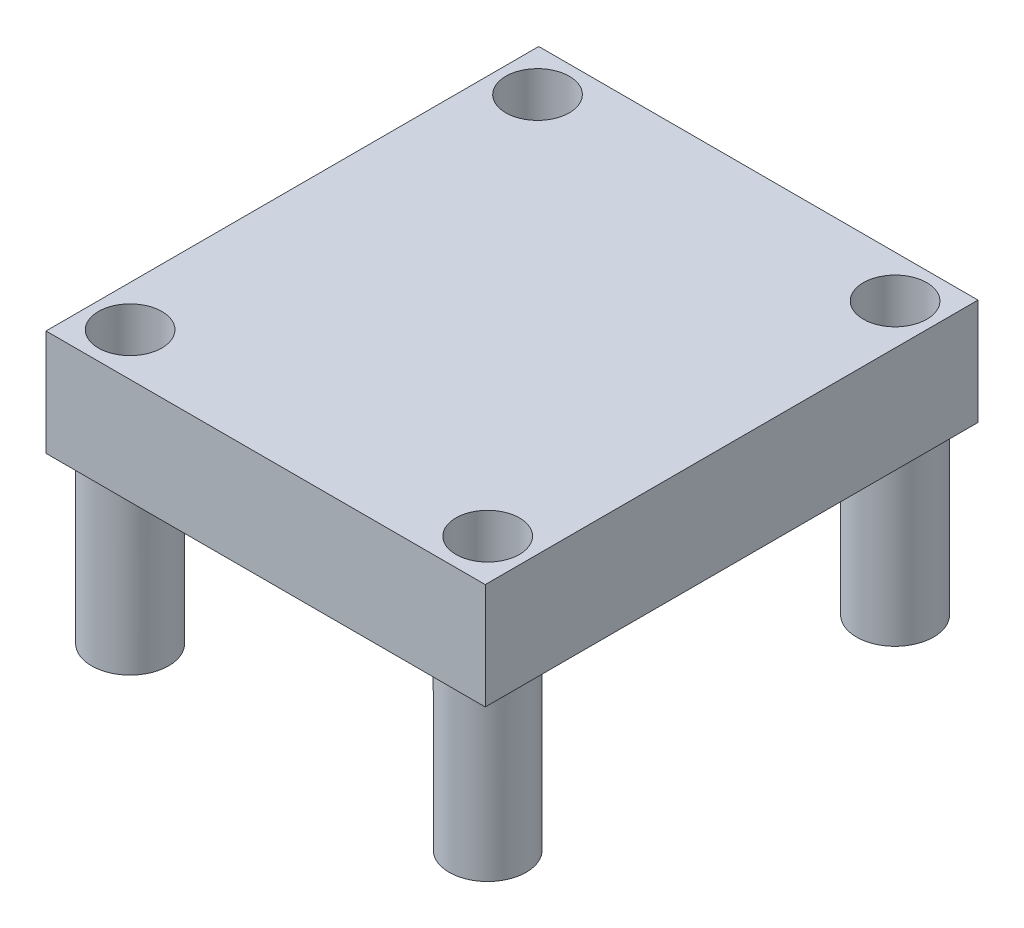
SolidWorks part; units mm, degrees
ref_plane "Front Plane" through (0, 0, 0) normal (0, 0, 1) x (1, 0, 0)
ref_plane "Top Plane" through (0, 0, 0) normal (0, 1, 0) x (1, 0, 0)
ref_plane "Right Plane" through (0, 0, 0) normal (1, 0, 0) x (0, 0, -1)
sketch "Sketch1" plane through (0, 0, 0) normal (0, 1, 0) x (1, 0, 0)
  line L0 (-34.0407, 1.6731) -> (-34.0407, -23.8285)
  line L1 (-34.0407, -23.8285) -> (-11.3077, -23.8285)
  line L2 (-11.3077, -23.8285) -> (-11.3077, 1.6731)
  line L3 (-11.3077, 1.6731) -> (-34.0407, 1.6731)
  dimension "D1" = 25.5016
  dimension "D2" = 22.733
extrude "Boss-Extrude1" add sketch "Sketch1" along normal blind 5.4864
sketch "Sketch2" plane through (0, 0, 0) normal (0, -1, 0) x (1, 0, 0)
  circle A0 centre (-31.9185, 21.5968) radius 1.9939
  circle A1 centre (-13.4143, 21.5968) radius 1.9939
  circle A2 centre (-31.9185, 0.5117) radius 1.9939
  circle A3 centre (-13.4143, 0.5117) radius 1.9939
  circle A4 centre (-31.9185, 21.5968) radius 1.6424
  circle A5 centre (-31.9185, 0.5117) radius 1.6424
  circle A6 centre (-13.4143, 0.5117) radius 1.6424
  circle A7 centre (-13.4143, 21.5968) radius 1.6424
  point P4 (-31.9185, 0.4178)
  point P8 (-13.5081, 0.5117)
  point P12 (-13.5081, 21.5968)
  dimension "D1" = 3.9878
  dimension "D2" = 3.2848
extrude "Boss-Extrude2" add sketch "Sketch2" along normal blind 8.5852
sketch "Sketch5" plane through (0, 5.4864, 0) normal (0, 1, 0) x (1, 0, 0)
  circle A0 centre (-31.9185, -0.5117) radius 1.6424
  circle A1 centre (-13.4143, -0.5117) radius 1.6424
  circle A2 centre (-13.4143, -21.5968) radius 1.6424
  circle A3 centre (-31.9185, -21.5968) radius 1.6424
extrude "Cut-Extrude1" cut sketch "Sketch5" against normal through all both and the other way through all
